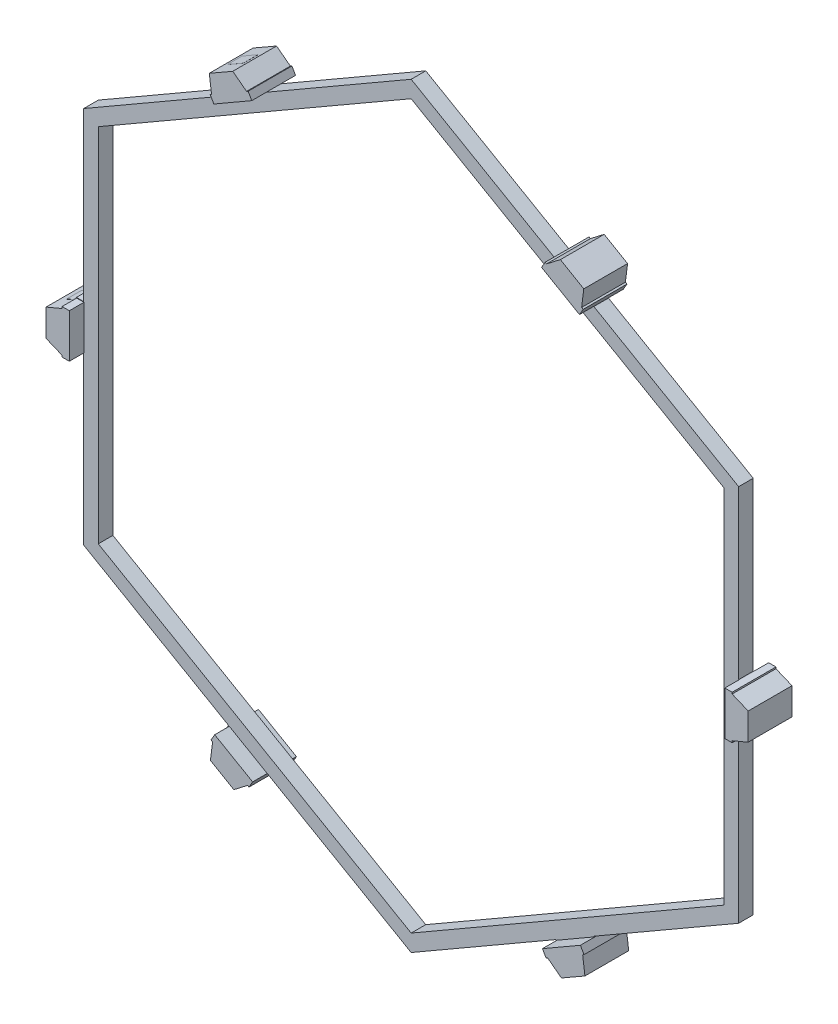
SolidWorks part; units mm, degrees
ref_plane "Front Plane" through (0, 0, 0) normal (0, 0, 1) x (1, 0, 0)
ref_plane "Top Plane" through (0, 0, 0) normal (0, 1, 0) x (1, 0, 0)
ref_plane "Right Plane" through (0, 0, 0) normal (1, 0, 0) x (0, 0, -1)
sketch "Sketch1" plane through (0, 0, 0) normal (0, 0, 1) x (1, 0, 0)
  line L1 (22.397, 12.9524) -> (12.477, 18.6797)
  line L2 (-0.0371, 25.9047) -> (-9.9572, 20.1774)
  line L3 (-22.4712, 12.9524) -> (-22.4712, 1.9011)
  line L4 (-22.4712, -12.9523) -> (-12.6301, -18.6341)
  line L5 (-0.0371, -25.9047) -> (9.7907, -20.2306)
  line L6 (22.397, -12.9523) -> (22.397, -1.4976)
  line L7 (21.397, 12.375) -> (-0.0371, 24.75)
  line L8 (-0.0371, 24.75) -> (-21.4712, 12.375)
  line L9 (-21.4712, 12.375) -> (-21.4712, -12.375)
  line L10 (-21.4712, -12.375) -> (-0.0371, -24.75)
  line L11 (-0.0371, -24.75) -> (21.397, -12.375)
  line L12 (21.397, -12.375) -> (21.397, 12.375)
  line L37 (22.397, 1.5024) -> (22.397, 12.9524)
  line L54 (-12.5553, 18.6774) -> (-12.8053, 19.1104)
  line L55 (-9.9572, 20.1774) -> (-10.2072, 20.6104)
  line L56 (-12.8053, 19.1104) -> (-12.6181, 19.2185)
  line L57 (-12.6295, 20.482) -> (-11.53, 21.1168)
  line L58 (-10.4179, 20.4887) -> (-10.2072, 20.6104)
  line L64 (12.5491, -18.638) -> (22.397, -12.9523)
  line L65 (-9.9313, -20.1923) -> (-0.0371, -25.9047)
  line L66 (-22.4712, -1.5964) -> (-22.4712, -12.9523)
  line L67 (-12.5553, 18.6774) -> (-22.4712, 12.9524)
  line L68 (9.8789, 20.1797) -> (-0.0371, 25.9047)
  line L69 (12.477, 18.6797) -> (12.727, 19.1127)
  line L70 (12.5162, 19.2344) -> (12.727, 19.1127)
  line L71 (11.4046, 21.1464) -> (12.5041, 20.5116)
  line L72 (9.8789, 20.1797) -> (10.1289, 20.6127)
  line L73 (10.1289, 20.6127) -> (10.3161, 20.5047)
  line L74 (22.397, -1.4976) -> (22.897, -1.4976)
  line L75 (22.897, -1.2543) -> (22.897, -1.4976)
  line L76 (23.997, 0.6644) -> (23.997, -0.6052)
  line L77 (22.397, 1.5024) -> (22.897, 1.5024)
  line L78 (22.897, 1.5024) -> (22.897, 1.2862)
  line L79 (9.8829, -20.1773) -> (10.1329, -20.6103)
  line L80 (10.3437, -20.4887) -> (10.1329, -20.6103)
  line L81 (12.5553, -20.482) -> (11.4558, -21.1167)
  line L82 (12.481, -18.6773) -> (12.731, -19.1103)
  line L83 (12.731, -19.1103) -> (12.5438, -19.2184)
  line L84 (-12.5512, -18.6797) -> (-12.8012, -19.1127)
  line L85 (-12.5904, -19.2344) -> (-12.8012, -19.1127)
  line L86 (-11.4788, -21.1463) -> (-12.5783, -20.5115)
  line L87 (-9.9531, -20.1797) -> (-10.2031, -20.6127)
  line L88 (-10.2031, -20.6127) -> (-10.3903, -20.5046)
  line L89 (-22.4712, 1.4977) -> (-22.9712, 1.4977)
  line L90 (-22.9712, 1.2543) -> (-22.9712, 1.4977)
  line L91 (-24.0712, -0.6643) -> (-24.0712, 0.6053)
  line L92 (-22.4712, -1.5023) -> (-22.9712, -1.5023)
  line L93 (-22.9712, -1.5023) -> (-22.9712, -1.2862)
  line L94 (9.7907, -20.2306) -> (9.8829, -20.1773)
  line L95 (12.5491, -18.638) -> (12.481, -18.6773)
  line L96 (-9.9313, -20.1923) -> (-9.9531, -20.1797)
  line L97 (-22.4712, -1.5023) -> (-22.4712, -1.5964)
  line L98 (-22.4712, 1.9011) -> (-22.4712, 1.4977)
  line L99 (-12.6301, -18.6341) -> (-12.5512, -18.6797)
  arc A10 (-12.6181, 19.2185) -> (-12.6295, 20.482) centre (-11.5062, 19.8604) cw
  arc A11 (-11.53, 21.1168) -> (-10.4179, 20.4887) centre (-11.5062, 19.8604) cw
  arc A12 (12.5041, 20.5116) -> (12.5162, 19.2344) centre (11.4279, 19.8627) cw
  arc A13 (10.3161, 20.5047) -> (11.4046, 21.1464) centre (11.4279, 19.8627) cw
  arc A14 (23.997, -0.6052) -> (22.897, -1.2543) centre (22.897, 0.0024) cw
  arc A15 (22.897, 1.2862) -> (23.997, 0.6644) centre (22.897, 0.0024) cw
  arc A16 (11.4558, -21.1167) -> (10.3437, -20.4887) centre (11.432, -19.8603) cw
  arc A17 (12.5438, -19.2184) -> (12.5553, -20.482) centre (11.432, -19.8603) cw
  arc A18 (-12.5783, -20.5115) -> (-12.5904, -19.2344) centre (-11.5021, -19.8627) cw
  arc A19 (-10.3903, -20.5046) -> (-11.4788, -21.1463) centre (-11.5021, -19.8627) cw
  arc A20 (-24.0712, 0.6053) -> (-22.9712, 1.2543) centre (-22.9712, -0.0023) cw
  arc A21 (-22.9712, -1.2862) -> (-24.0712, -0.6643) centre (-22.9712, -0.0023) cw
  point P78 (-0.0371, 0)
  dimension "D1" = 0
  dimension "D2" = 1
  dimension "D9" = 1.1
  dimension "D5" = 1
  dimension "D8" = 1.2566
  dimension "D3" = 1
  dimension "D4" = 1
  dimension "D7" = 1
  dimension "D10" = 1.6
  dimension "D6" = 1
  dimension "D11" = 1.5
  dimension "D12" = 3
  dimension "D13" = 24.75
  dimension "D14" = 25.9047
  dimension "D15" = 24.75
  dimension "D16" = 11.45
  dimension "D17" = 6
extrude "Boss-Extrude1" add sketch "Sketch1" along normal blind 1
sketch "Sketch2" plane through (0, 0, 1) normal (0, 0, 1) x (1, 0, 0)
  line L0 (-12.5553, 18.6774) -> (-9.9572, 20.1774)
  line L1 (-9.9572, 20.1774) -> (-10.2072, 20.6104)
  line L2 (-10.2072, 20.6104) -> (-10.3126, 20.5496)
  line L3 (-12.8672, 20.3448) -> (-11.2585, 21.2681)
  line L4 (-11.53, 21.1168) -> (-12.6295, 20.482) construction
  line L5 (-12.5553, 18.6774) -> (-12.8053, 19.1104)
  line L6 (-12.8053, 19.1104) -> (-12.7117, 19.1644)
  line L7 (-12.7117, 19.1644) -> (-12.8672, 20.3448)
  line L8 (-11.2585, 21.2681) -> (-10.3126, 20.5496)
  line L9 (-12.6181, 19.2185) -> (-12.8053, 19.1104) construction
  line L10 (-10.2072, 20.6104) -> (-10.4179, 20.4887) construction
  line L11 (11.1855, 21.3157) -> (12.7894, 20.3841)
  line L12 (12.7894, 20.3841) -> (12.6402, 19.2057)
  line L13 (12.7455, 19.1449) -> (12.6402, 19.2057)
  line L14 (12.4955, 18.7119) -> (12.7455, 19.1449)
  line L15 (9.8975, 20.2119) -> (12.4955, 18.7119)
  line L16 (9.8975, 20.2119) -> (10.1475, 20.6449)
  line L17 (10.1475, 20.6449) -> (10.2411, 20.5908)
  line L18 (10.2411, 20.5908) -> (11.1855, 21.3157)
  line L19 (24.0527, 0.971) -> (24.0479, -0.8839)
  line L20 (24.0479, -0.8839) -> (22.9527, -1.3438)
  line L21 (22.9527, -1.4655) -> (22.9527, -1.3438)
  line L22 (22.4527, -1.4655) -> (22.9527, -1.4655)
  line L23 (22.4527, 1.5345) -> (22.4527, -1.4655)
  line L24 (22.4527, 1.5345) -> (22.9527, 1.5345)
  line L25 (22.9527, 1.5345) -> (22.9527, 1.4264)
  line L26 (22.9527, 1.4264) -> (24.0527, 0.971)
  line L27 (12.8672, -20.3448) -> (11.2585, -21.2681)
  line L28 (11.2585, -21.2681) -> (10.3126, -20.5496)
  line L29 (10.2072, -20.6104) -> (10.3126, -20.5496)
  line L30 (9.9572, -20.1774) -> (10.2072, -20.6104)
  line L31 (12.5553, -18.6774) -> (9.9572, -20.1774)
  line L32 (12.5553, -18.6774) -> (12.8053, -19.1104)
  line L33 (12.8053, -19.1104) -> (12.7117, -19.1644)
  line L34 (12.7117, -19.1644) -> (12.8672, -20.3448)
  line L35 (-11.1855, -21.3157) -> (-12.7894, -20.3841)
  line L36 (-12.7894, -20.3841) -> (-12.6402, -19.2057)
  line L37 (-12.7455, -19.1449) -> (-12.6402, -19.2057)
  line L38 (-12.4955, -18.7119) -> (-12.7455, -19.1449)
  line L39 (-9.8975, -20.2119) -> (-12.4955, -18.7119)
  line L40 (-9.8975, -20.2119) -> (-10.1475, -20.6449)
  line L41 (-10.1475, -20.6449) -> (-10.2411, -20.5908)
  line L42 (-10.2411, -20.5908) -> (-11.1855, -21.3157)
  line L43 (-24.0527, -0.971) -> (-24.0479, 0.8839)
  line L44 (-24.0479, 0.8839) -> (-22.9527, 1.3438)
  line L45 (-22.9527, 1.4655) -> (-22.9527, 1.3438)
  line L46 (-22.4527, 1.4655) -> (-22.9527, 1.4655)
  line L47 (-22.4527, -1.5345) -> (-22.4527, 1.4655)
  line L48 (-22.4527, -1.5345) -> (-22.9527, -1.5345)
  line L49 (-22.9527, -1.5345) -> (-22.9527, -1.4264)
  line L50 (-22.9527, -1.4264) -> (-24.0527, -0.971)
  point P64 (0, 0)
  dimension "D1" = 6
extrude "Boss-Extrude2" add sketch "Sketch2" along normal blind 1 and the other way blind 2
